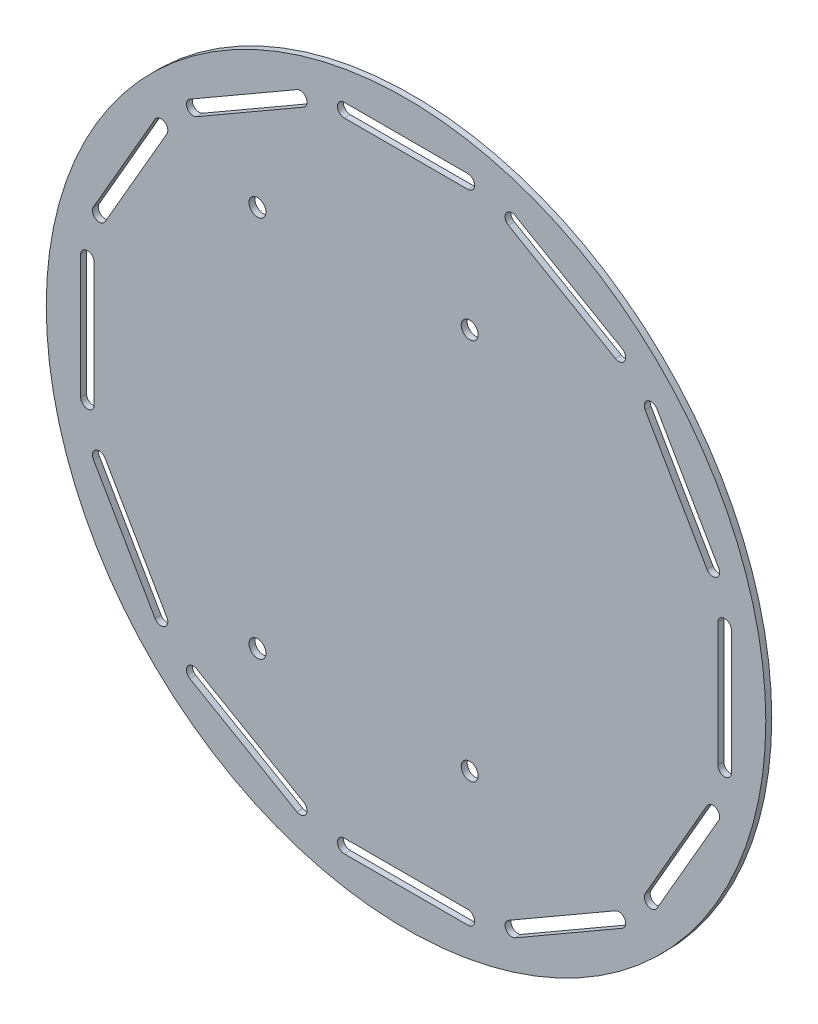
SolidWorks part; units mm, degrees
material "3.3535 (EN-AW 5754)"
ref_plane "Front" through (0, 0, 0) normal (0, 0, 1) x (1, 0, 0)
ref_plane "Top" through (0, 0, 0) normal (0, 1, 0) x (1, 0, 0)
ref_plane "Right" through (0, 0, 0) normal (1, 0, 0) x (0, 0, -1)
sketch "Эскиз1" plane through (0, 0, 0) normal (0, 0, 1) x (1, 0, 0)
  line L0 (0, 0) -> (0, 26.6616) construction
  line L1 (0, 0) -> (-24.5807, 0) construction
  line L2 (0, -45) -> (0, 45) construction
  line L3 (0, 45) -> (15, 45) construction
  line L4 (0, 45) -> (-35, 45) construction
  line L5 (0, -45) -> (-35, -45) construction
  line L6 (0, -45) -> (15, -45) construction
  line L7 (-35, 45) -> (-35, -45) construction
  circle A0 centre (0, 0) radius 84.75
  circle A2 centre (15, 45) radius 2
  circle A3 centre (-35, 45) radius 2
  circle A4 centre (-35, -45) radius 2
  circle A5 centre (15, -45) radius 2
  dimension "D1" = 169.5
  dimension "D2" = 50
  dimension "D3" = 35
  dimension "D4" = 50
  dimension "D5" = 15
extrude "Бобышка-Вытянуть1" add sketch "Эскиз1" along normal blind 1.4
sketch "Эскиз2" plane through (0, 0, 1.4) normal (0, 0, 1) x (1, 0, 0)
  line L0 (73.45, -14.55) -> (73.45, 14.55)
  line L2 (76.65, -14.55) -> (76.65, 14.55)
  line L3 (0, 0) -> (16.5568, 0) construction
  line L4 (0, 0) -> (0, 11.9695) construction
  line L6 (73.45, 0) -> (76.65, 0) construction
  line L7 (75.05, -14.55) -> (75.05, 14.55) construction
  circle A0 centre (0, 0) radius 76.65 construction
  circle A1 centre (0, 0) radius 73.45 construction
  arc A7 (76.65, 14.55) -> (73.45, 14.55) centre (75.05, 14.55) ccw
  arc A8 (76.65, -14.55) -> (73.45, -14.55) centre (75.05, -14.55) cw
  point P6 (75.05, 0)
  point P7 (73.45, 0)
  point P23 (76.65, 0)
  dimension "D3" = 153.3
  dimension "D4" = 146.9
extrude "Вырез-Вытянуть1" cut sketch "Эскиз2" against normal blind 1.4
pattern_circular "Круговой массив1" count 12 over 360 about axis through (0, 0, 0) along (0, 0, 1) of "Вырез-Вытянуть1"
sketch "Эскиз3" plane through (0, 0, 1.4) normal (0, 0, 1) x (1, 0, 0)
  circle A2 centre (75.05, 0) radius 1.6
  circle A4 centre (75.05, 14.55) radius 1.6
  circle A5 centre (75.05, -14.55) radius 1.6
  circle A8 centre (64.9952, -37.525) radius 1.6
  circle A9 centre (72.2702, -24.9243) radius 1.6
  circle A10 centre (57.7202, -50.1257) radius 1.6
  circle A11 centre (37.525, -64.9952) radius 1.6
  circle A12 centre (50.1257, -57.7202) radius 1.6
  circle A13 centre (24.9243, -72.2702) radius 1.6
  circle A14 centre (0, -75.05) radius 1.6
  circle A15 centre (14.55, -75.05) radius 1.6
  circle A16 centre (-14.55, -75.05) radius 1.6
  circle A17 centre (-37.525, -64.9952) radius 1.6
  circle A18 centre (-24.9243, -72.2702) radius 1.6
  circle A19 centre (-50.1257, -57.7202) radius 1.6
  circle A20 centre (-64.9952, -37.525) radius 1.6
  circle A21 centre (-57.7202, -50.1257) radius 1.6
  circle A22 centre (-72.2702, -24.9243) radius 1.6
  circle A23 centre (-75.05, 0) radius 1.6
  circle A24 centre (-75.05, -14.55) radius 1.6
  circle A25 centre (-75.05, 14.55) radius 1.6
  circle A26 centre (-64.9952, 37.525) radius 1.6
  circle A27 centre (-72.2702, 24.9243) radius 1.6
  circle A28 centre (-57.7202, 50.1257) radius 1.6
  circle A29 centre (-37.525, 64.9952) radius 1.6
  circle A30 centre (-50.1257, 57.7202) radius 1.6
  circle A31 centre (-24.9243, 72.2702) radius 1.6
  circle A32 centre (0, 75.05) radius 1.6
  circle A33 centre (-14.55, 75.05) radius 1.6
  circle A34 centre (14.55, 75.05) radius 1.6
  circle A35 centre (37.525, 64.9952) radius 1.6
  circle A36 centre (24.9243, 72.2702) radius 1.6
  circle A37 centre (50.1257, 57.7202) radius 1.6
  circle A38 centre (64.9952, 37.525) radius 1.6
  circle A39 centre (57.7202, 50.1257) radius 1.6
  circle A40 centre (72.2702, 24.9243) radius 1.6
  point P81 (0, 0)
  dimension "D1" = 12
